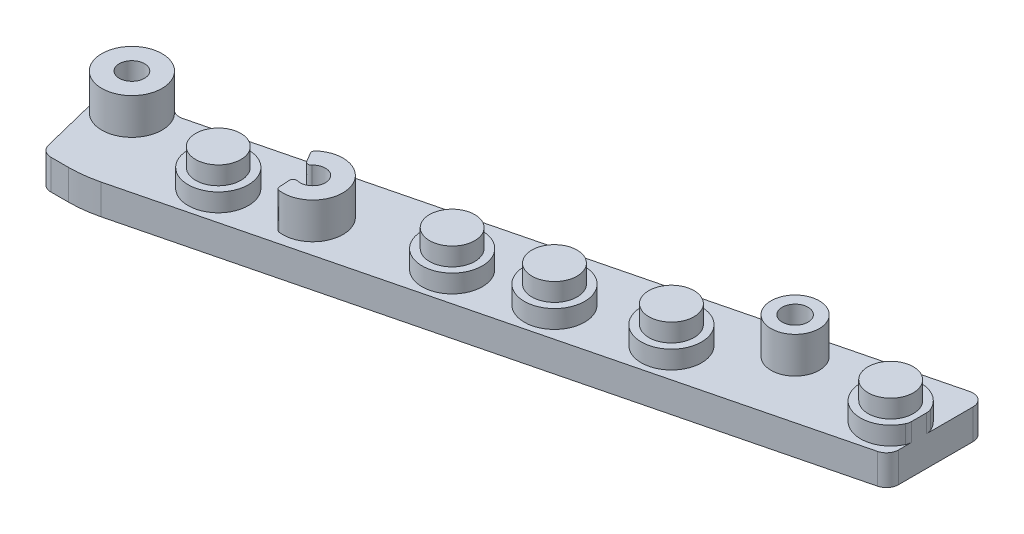
SolidWorks part; units mm, degrees
ref_plane "Front Plane" through (0, 0, 0) normal (0, 0, 1) x (1, 0, 0)
ref_plane "Top Plane" through (0, 0, 0) normal (0, 1, 0) x (1, 0, 0)
ref_plane "Right Plane" through (0, 0, 0) normal (1, 0, 0) x (0, 0, -1)
sketch "Sketch1" plane through (0, 0, 0) normal (0, 1, 0) x (-1, 0, 0)
  line L0 (27.94, 12.7851) -> (25.619, 22.0941) construction
  line L2 (132.8591, 54.0676) -> (1.9255, 21.4222)
  line L4 (137.8622, 47.4617) -> (6.0087, 14.5869) construction
  line L5 (3.1545, 0.7865) -> (135.8682, 33.8757)
  line L7 (148.4014, 39.7213) -> (145.1164, 52.8965)
  line L8 (148.4824, 37.0208) -> (398.1253, 99.2638)
  line L9 (0, 18.9576) -> (0, 3.2511)
  line L10 (139.0039, 54.8221) -> (142.6519, 54.8221)
  circle A0 centre (42.977, 23.8042) radius 11.1125 construction
  circle A1 centre (79.9452, 33.0214) radius 11.1125 construction
  circle A2 centre (119.3781, 42.8531) radius 11.1125 construction
  circle A3 centre (6.0087, 14.5869) radius 11.1125 construction
  circle A7 centre (142.24, 38.1851) radius 2.667
  circle A8 centre (27.94, 12.7851) radius 2.667
  circle A9 centre (104.14, 38.1851) radius 2.667
  arc A11 (138.1276, 33.3466) -> (148.4014, 39.7213) centre (142.24, 38.1851) ccw
  arc A15 (135.8682, 33.8757) -> (138.1276, 33.3466) centre (136.4827, 31.4112) cw
  arc A16 (145.1164, 52.8965) -> (142.6519, 54.8221) centre (142.6519, 52.2821) ccw
  arc A17 (3.1545, 0.7865) -> (0, 3.2511) centre (2.54, 3.2511) cw
  arc A18 (0, 18.9576) -> (1.9255, 21.4222) centre (2.54, 18.9576) cw
  arc A19 (132.8591, 54.0676) -> (139.0039, 54.8221) centre (139.0039, 29.4221) cw
  point P19 (137.2749, 34.2265)
  point P27 (144.6363, 54.8221)
  point P33 (0, 0)
  point P37 (0, 20.9421)
  point P40 (135.8852, 54.8221)
  dimension "D1" = 19.05
  dimension "D5" = 38.1
  dimension "D6" = 22.225
  dimension "D9" = 12.7851
  dimension "D10" = 141.4774
  dimension "D11" = 12.7
  dimension "D12" = 5.334
  dimension "D13" = 6.35
  dimension "D14" = 140.0451
  dimension "D15" = 104.14
  dimension "D18" = 27.94
  dimension "D19" = 38.1851
  dimension "D20" = 2.54
  dimension "D21" = 25.4
  dimension "D22" = 5.08
  dimension "D2" = 8.3535
  dimension "D3" = 40.64
  dimension "D4" = 38.1
  dimension "D7" = 104
  dimension "D8" = 7.62
  dimension "D16" = 8.7511
  dimension "D17" = 15.5631
extrude "Boss-Extrude1" add sketch "Sketch1" against normal blind 6.35
sketch "Sketch3" plane through (0, -6.35, 0) normal (0, -1, 0) x (-1, 0, 0)
  line L0 (0, -13.0108) -> (0, -16.163)
  line L1 (6.0087, -14.5869) -> (119.3781, -42.8531) construction
  line L4 (0, 55) -> (0, -55) construction
  line L13 (-55, 0) -> (55, 0) construction
  circle A20 centre (6.0087, -14.5869) radius 11.1125 construction
  circle A21 centre (119.3781, -42.8531) radius 11.1125 construction
  circle A22 centre (79.9452, -33.0214) radius 11.1125 construction
  circle A23 centre (42.977, -23.8042) radius 11.1125 construction
  arc A33 (0.2275, -17.2138) -> (0.2275, -11.9601) centre (6.0087, -14.5869) ccw
  circle A34 centre (42.977, -23.8042) radius 6.35
  circle A35 centre (79.9452, -33.0214) radius 6.35
  circle A36 centre (119.3781, -42.8531) radius 6.35
  circle A37 centre (62.6934, -28.72) radius 6.35
  arc A38 (0.2275, -17.2138) -> (0, -16.163) centre (2.54, -16.163) cw
  arc A39 (0.2275, -11.9601) -> (0, -13.0108) centre (2.54, -13.0108) ccw
  dimension "D1" = 38.1
  dimension "D5" = 14.5869
  dimension "D6" = 14
  dimension "D7" = 12.7
  dimension "D8" = 2.54
  dimension "D2" = 38.1
  dimension "D3" = 40.64
  dimension "D4" = 6.0087
extrude "Boss-Extrude2" add sketch "Sketch3" along normal blind 3.81
sketch "Sketch4" plane through (0, -10.16, 0) normal (0, -1, 0) x (1, 0, 0)
  circle A0 centre (-6.0087, 14.5869) radius 4.7625
  circle A1 centre (-42.977, 23.8042) radius 4.7625
  circle A2 centre (-62.6934, 28.72) radius 4.7625
  circle A3 centre (-79.9452, 33.0214) radius 4.7625
  circle A4 centre (-119.3781, 42.8531) radius 4.7625
  dimension "D1" = 9.525
extrude "Boss-Extrude3" add sketch "Sketch4" along normal blind 3.81
sketch "Sketch5" plane through (0, -6.35, 0) normal (0, -1, 0) x (1, 0, 0)
  line L0 (-105.5802, 43.778) -> (-105.7153, 41.5623)
  line L1 (-107.3366, 36.2697) -> (-108.4657, 34.3585)
  circle A4 centre (-142.24, 38.1851) radius 6.35
  arc A5 (-108.3101, 33.3962) -> (-104.9122, 44.4879) centre (-104.14, 38.1851) ccw
  circle A7 centre (-27.94, 12.7851) radius 5.08
  circle A9 centre (-104.14, 38.1851) radius 2.667 construction
  arc A10 (-106.116, 36.3939) -> (-104.7737, 40.7757) centre (-104.14, 38.1851) ccw
  circle A11 centre (-142.24, 38.1851) radius 2.667
  circle A13 centre (-27.94, 12.7851) radius 2.724
  arc A15 (-108.3101, 33.3962) -> (-108.4657, 34.3585) centre (-107.8097, 33.9709) cw
  arc A16 (-107.3366, 36.2697) -> (-106.116, 36.3939) centre (-106.6806, 35.8821) cw
  arc A17 (-104.7737, 40.7757) -> (-105.7153, 41.5623) centre (-104.9547, 41.5159) cw
  arc A18 (-104.9122, 44.4879) -> (-105.5802, 43.778) centre (-104.8196, 43.7316) ccw
  point P35 (-106.6819, 37.3779)
  point P38 (-105.7937, 40.2775)
  dimension "D1" = 12.7
  dimension "D2" = 2.2157
  dimension "D4" = 1.778
  dimension "D3" = 1.778
  dimension "D7" = 0.762
  dimension "D6" = 5.334
  dimension "D9" = 10.16
  dimension "D11" = 5.4479
  dimension "D5" = 1.9112
extrude "Boss-Extrude4" add sketch "Sketch5" along direction (0, -1, 0) on the side of the normal up to surface (7.62 mm away)
mirror "Mirror6" about plane through (-139.0039, 0, 29.4221) normal (0, -1, 0) of "Boss-Extrude4", "Boss-Extrude3", "Boss-Extrude2", "Boss-Extrude1"
sketch "Sketch6" plane through (0, 0, 0) normal (1, 0, 0) x (0, 0, -1)
  line L0 (-54.8221, -6.35) -> (-54.8221, 6.35) construction
  line L1 (-54.8221, 0) -> (0, 0)
  line L2 (-54.8221, 0) -> (-54.8221, -25.4)
  line L3 (-54.8221, -25.4) -> (0, -25.4)
  line L4 (0, 0) -> (0, -25.4)
  line L5 (0, 55) -> (0, -55) construction
  dimension "D1" = 25.4
extrude "Cut-Extrude2" cut sketch "Sketch6" against normal blind 156.972 and the other way blind 10.414
